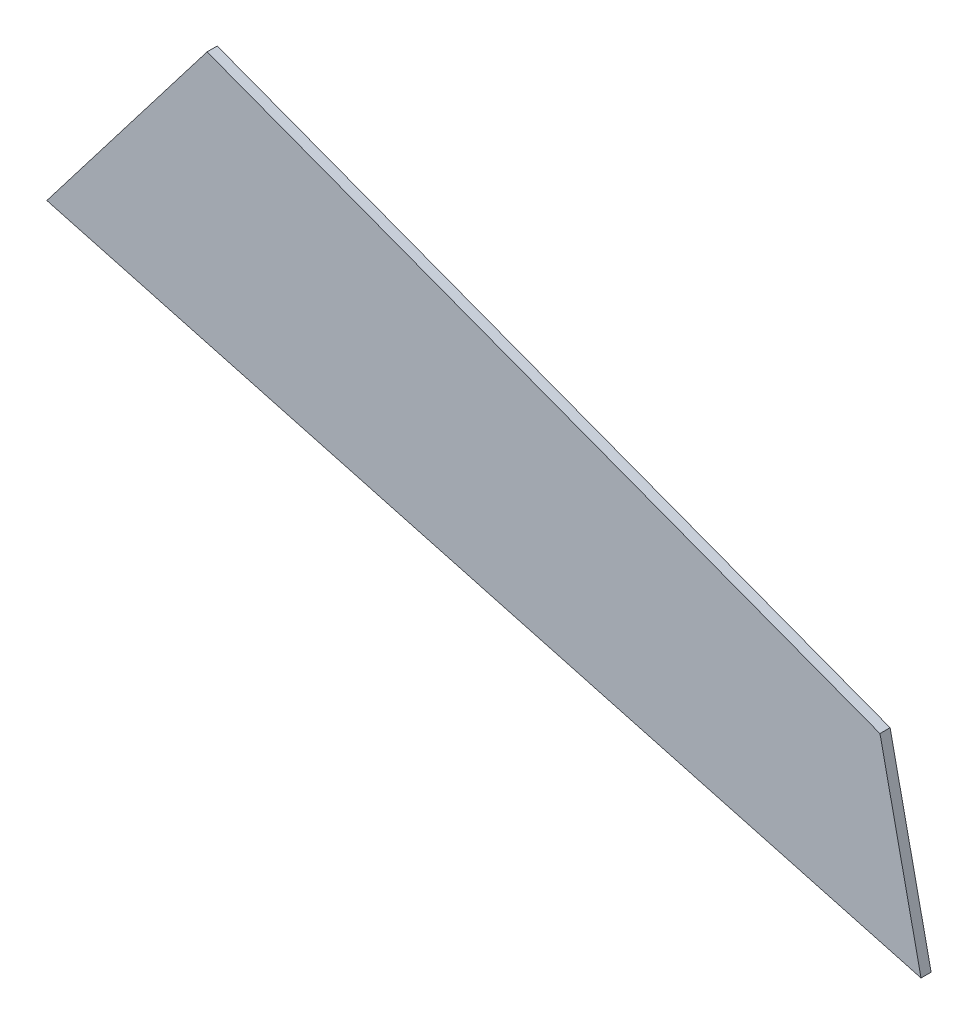
SolidWorks part; units mm, degrees
ref_plane "Plan de face" through (0, 0, 0) normal (0, 0, 1) x (1, 0, 0)
ref_plane "Plan de dessus" through (0, 0, 0) normal (0, 1, 0) x (1, 0, 0)
ref_plane "Plan de droite" through (0, 0, 0) normal (1, 0, 0) x (0, 0, -1)
sketch "Esquisse1" plane through (0, 0, 0) normal (0, 0, 1) x (1, 0, 0)
  line L0 (-484.4893, 49.9278) -> (-436.9882, 111.8465)
  line L1 (-436.9882, 111.8465) -> (-237.514, 36.5694)
  line L2 (-237.514, 36.5694) -> (-225.3402, -20.1066)
  line L3 (-225.3402, -20.1066) -> (-484.4893, 49.9278)
  line L4 (-484.4893, 49.9278) -> (-225.3402, -20.1066) construction
  point P4 (-503.9513, 41.7661)
  point P9 (-508.9122, 21.7314)
  point P11 (-515.0361, 13.7169)
  point P15 (-448.3479, 116.377)
  point P16 (-437.1631, 112.8632)
  point P17 (-432.2436, 110.7576)
  point P18 (0, 0)
  point P19 (-438.1184, 114.0511)
  point P20 (-436.9535, 113.6012)
  point P21 (-436.9882, 111.8465)
extrude "Boss.-Extru.1" add sketch "Esquisse1" along normal blind 3
